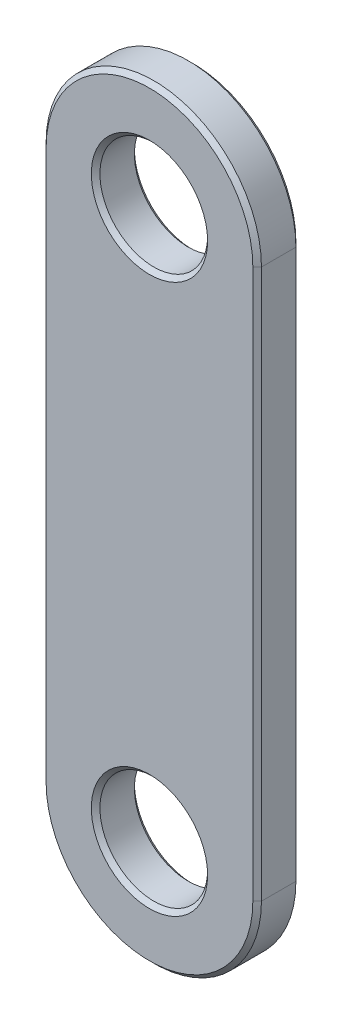
SolidWorks part; units mm, degrees
ref_plane "Front Plane" through (0, 0, 0) normal (0, 0, 1) x (1, 0, 0)
ref_plane "Top Plane" through (0, 0, 0) normal (0, 1, 0) x (1, 0, 0)
ref_plane "Right Plane" through (0, 0, 0) normal (1, 0, 0) x (0, 0, -1)
sketch "Sketch2" plane through (0, 0, 0) normal (0, 0, 1) x (1, 0, 0)
  line L0 (-330.5817, 0) -> (324.9307, 0) construction
  line L1 (0, 338.2105) -> (0, -175.5332) construction
  line L2 (0, 127.5) -> (0, -127.5) construction
  line L3 (50, 127.5) -> (50, -127.5)
  line L4 (-50, 127.5) -> (-50, -127.5)
  arc A0 (50, 127.5) -> (-50, 127.5) centre (0, 127.5) ccw
  arc A1 (-50, -127.5) -> (50, -127.5) centre (0, -127.5) ccw
  circle A2 centre (0, 127.5) radius 25
  circle A3 centre (0, -127.5) radius 25
  point P7 (0, 0)
  dimension "D2" = 50
  dimension "D1" = 255
  dimension "D3" = 100
extrude "Boss-Extrude1" add sketch "Sketch2" along normal blind 20
chamfer "Chamfer1" distance 2 angle 45 12 edges at (25, -127.5, 0) (25, 127.5, 0) (50, 0, 0) (0, -177.5, 0) (-50, 0, 0) (0, 177.5, 0) (25, -127.5, 20) (25, 127.5, 20) (50, 0, 20) (0, -177.5, 20) (-50, 0, 20) (0, 177.5, 20)
